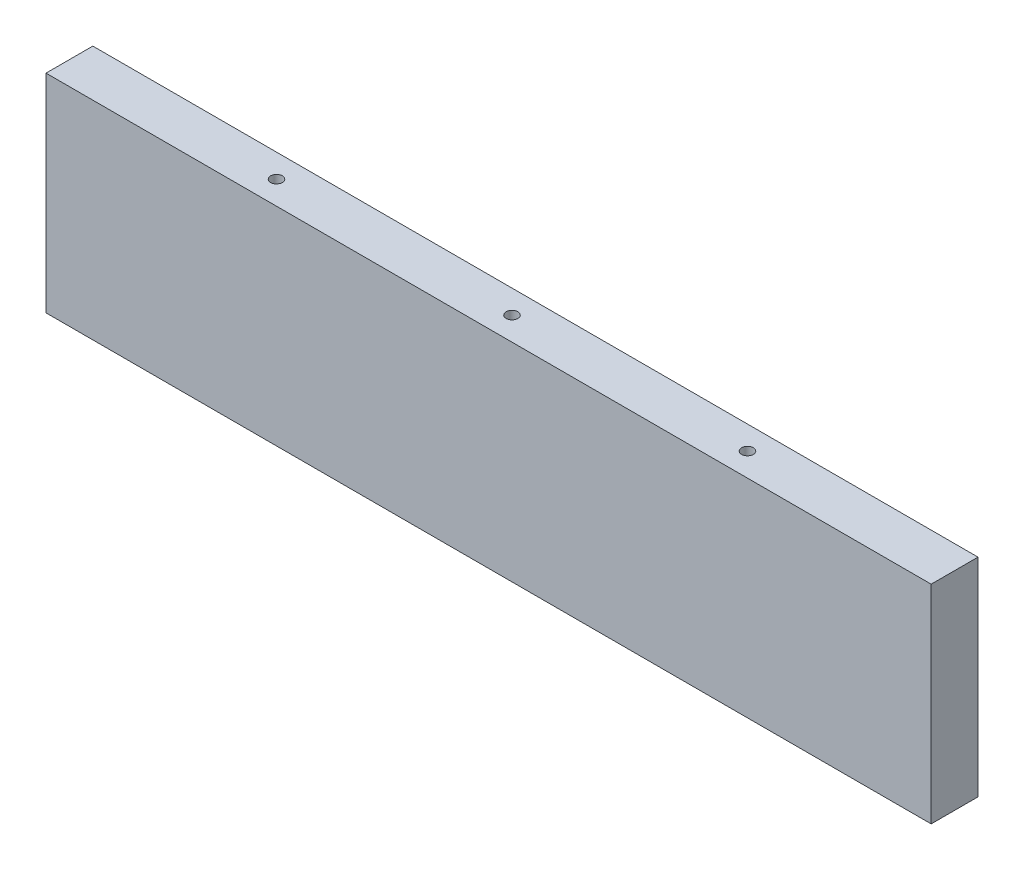
SolidWorks part; units mm, degrees
material "Beech"
ref_plane "Front Plane" through (0, 0, 0) normal (0, 0, 1) x (1, 0, 0)
ref_plane "Top Plane" through (0, 0, 0) normal (0, 1, 0) x (1, 0, 0)
ref_plane "Right Plane" through (0, 0, 0) normal (1, 0, 0) x (0, 0, -1)
sketch "Sketch1" plane through (0, 0, 0) normal (0, 0, 1) x (1, 0, 0)
  line L1 (-16.7045, 12.7) -> (-231.3045, 12.7)
  line L2 (-16.7045, 12.7) -> (-16.7045, 69)
  line L3 (-16.7045, 69) -> (-231.3045, 69)
  line L4 (-231.3045, 12.7) -> (-231.3045, 69)
  line L5 (-16.7045, 12.7) -> (-16.7045, 0) construction
  dimension "D1" = 56.3
extrude "Boss-Extrude1" add sketch "Sketch1" against normal blind 12.7
sketch "Sketch3" plane through (-231.3045, 0, 0) normal (-1, 0, 0) x (0, 0, 1)
  line L4 (0, 12.7) -> (0, 69)
  line L5 (0, 69) -> (-12.7, 69)
  line L6 (-12.7, 69) -> (-12.7, 12.7)
  line L7 (-12.7, 12.7) -> (0, 12.7)
  line L8 (0, 12.7) -> (0, 69)
  line L9 (0, 69) -> (-12.7, 69)
  line L10 (-12.7, 69) -> (-12.7, 12.7)
  line L11 (-12.7, 12.7) -> (0, 12.7)
  dimension "D1" = 0
extrude "Boss-Extrude2" add sketch "Sketch3" along normal blind 12.7
sketch "Sketch4" plane through (-16.7045, 0, 0) normal (1, 0, 0) x (0, 0, -1)
  line L4 (0, 69) -> (0, 12.7)
  line L5 (0, 12.7) -> (12.7, 12.7)
  line L6 (12.7, 12.7) -> (12.7, 69)
  line L7 (12.7, 69) -> (0, 69)
  line L8 (0, 69) -> (0, 12.7)
  line L9 (0, 12.7) -> (12.7, 12.7)
  line L10 (12.7, 12.7) -> (12.7, 69)
  line L11 (12.7, 69) -> (0, 69)
  dimension "D1" = 0
extrude "Boss-Extrude3" add sketch "Sketch4" along normal blind 12.7
hole_wizard "Hole1" positions "Sketch5" profile "Sketch6" legacy
sketch "Sketch5" plane through (-124.0045, 0, 155.0243) normal (0, -1, 0) x (-1, 0, 0)
  line L1 (0, 465.9538) -> (0, 167.7243) construction
  point P1 (113.65, 128.8076)
  point P3 (113.65, 23.941)
  point P5 (-94.6, 161.3743)
  point P7 (94.6, 161.3743)
  point P9 (0, 161.3743)
  point P11 (0, 193.1243)
  point P13 (0, 440.5538)
  point P15 (0, 301.9704)
  point P17 (40.9792, 301.9704)
  point P19 (166.7958, 301.9704)
  point P21 (207.775, 440.5538)
  point P23 (207.775, 333.0214)
  point P25 (207.775, 225.489)
  point P27 (207.775, 137.4243)
  point P29 (207.775, 10.4243)
  point P33 (-207.775, 10.4243)
  point P34 (-207.775, 137.4243)
  point P35 (-207.775, 225.489)
  point P36 (-207.775, 333.0214)
  point P37 (-207.775, 440.5538)
  point P38 (-166.7958, 301.9704)
  point P39 (-40.9792, 301.9704)
  point P40 (-113.65, 23.941)
  point P41 (-113.65, 128.8076)
sketch "Sketch6" plane through (-237.6545, 0, 26.2167) normal (1, 0, 0) x (0, 0, -1)
  line L0 (0, 0) -> (0, 32.7039)
  line L1 (0, 32.7039) -> (1.5875, 31.75)
  line L2 (1.5875, 31.75) -> (1.5875, 4.0177)
  line L3 (1.5875, 4.0177) -> (5.08, 0)
  line L4 (5.08, 0) -> (0, 0)
  line L5 (0, -14.3089) -> (0, 102.4216) construction
  line L6 (0, 32.7039) -> (-1.5875, 31.75) construction
  line L7 (-1.5875, 4.0177) -> (-5.08, 0) construction
  dimension "Diameter" = 3.175
  dimension "Depth" = 31.75
  dimension "C-Sink Diameter" = 10.16
  dimension "C-Sink Angle" = 82
  dimension "Drill Angle" = 118
hole_wizard "Hole2" positions "Sketch7" profile "Sketch8" legacy
sketch "Sketch7" plane through (-124.0045, 88.05, 155.0243) normal (0, 1, 0) x (1, 0, 0)
  point P15 (-162.3, -8.6257)
  point P34 (-113.65, 50.1576)
  point P36 (-113.65, 102.591)
  point P54 (162.3, -8.6257)
  point P55 (113.65, 50.1576)
  point P56 (113.65, 102.591)
  point P71 (63.85, 161.3743)
  point P73 (0, 161.3743)
  point P74 (-63.85, 161.3743)
sketch "Sketch8" plane through (-286.3045, 88.05, 163.65) normal (1, 0, 0) x (0, 0, 1)
  line L0 (0, 0) -> (0, 32.7039)
  line L1 (0, 32.7039) -> (1.5875, 31.75)
  line L2 (1.5875, 31.75) -> (1.5875, 4.0177)
  line L3 (1.5875, 4.0177) -> (5.08, 0)
  line L4 (5.08, 0) -> (0, 0)
  line L5 (0, -14.3089) -> (0, 102.4216) construction
  line L6 (0, 32.7039) -> (-1.5875, 31.75) construction
  line L7 (-1.5875, 4.0177) -> (-5.08, 0) construction
  dimension "Diameter" = 3.175
  dimension "Depth" = 31.75
  dimension "C-Sink Diameter" = 10.16
  dimension "C-Sink Angle" = 82
  dimension "Drill Angle" = 118
